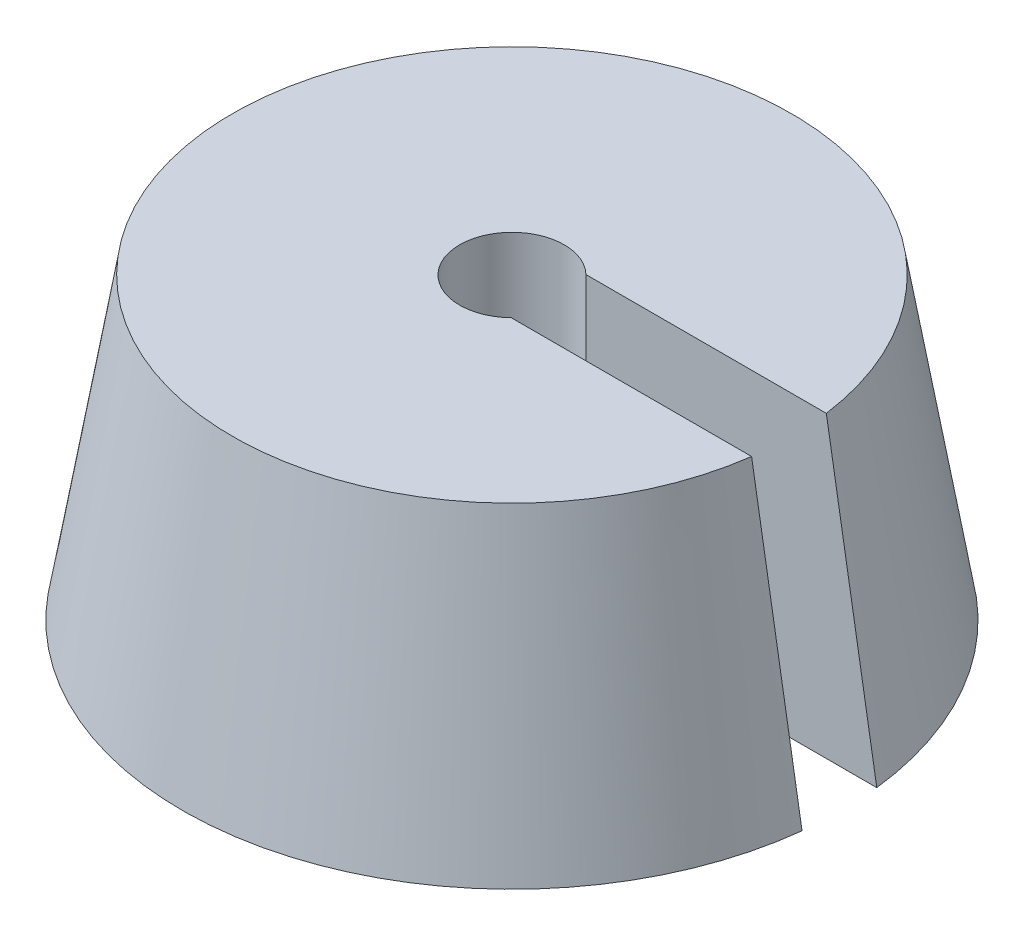
SolidWorks part; units mm, degrees
ref_plane "정면" through (0, 0, 0) normal (0, 0, 1) x (1, 0, 0)
ref_plane "윗면" through (0, 0, 0) normal (0, 1, 0) x (1, 0, 0)
ref_plane "우측면" through (0, 0, 0) normal (1, 0, 0) x (0, 0, -1)
sketch "스케치1" plane through (0, 0, 0) normal (0, 1, 0) x (1, 0, 0)
  circle A0 centre (0, 0) radius 22.05
  dimension "D1" = 44.1
ref_plane "평면1" through (0, 20, 0) normal (0, 1, 0) x (1, 0, 0)
sketch "스케치2" plane through (0, 20, 0) normal (0, 1, 0) x (1, 0, 0)
  circle A0 centre (0, 0) radius 18.7
  dimension "D1" = 37.4
loft "로프트1" add profiles "스케치1", "스케치2"
sketch "스케치5" plane through (0, 20, 0) normal (0, 1, 0) x (1, 0, 0)
  line L1 (0, 2.5) -> (26.5904, 2.5)
  line L2 (0, 2.5) -> (0, -2.5)
  line L3 (0, -2.5) -> (26.5904, -2.5)
  line L4 (26.5904, 2.5) -> (26.5904, -2.5)
  circle A0 centre (0, 0) radius 3.5
  point P7 (0, 0)
  dimension "D1" = 7
  dimension "D2" = 5
extrude "컷-돌출2" cut sketch "스케치5" against normal through all both and the other way through all
